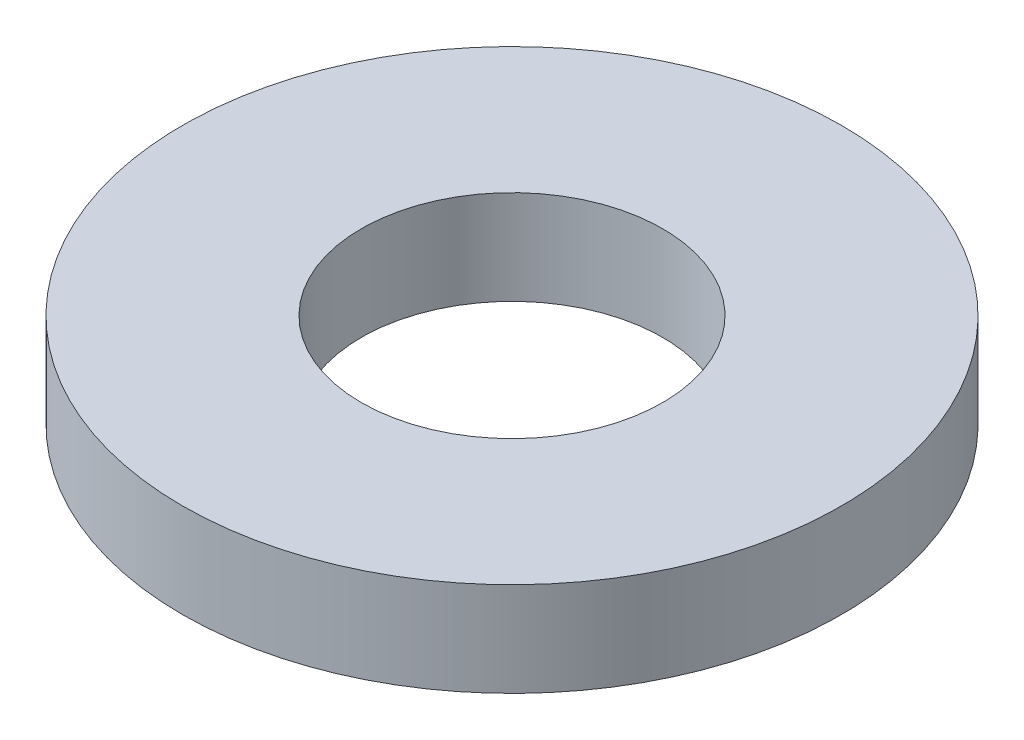
SolidWorks part; units mm, degrees
ref_plane "Front Plane" through (0, 0, 0) normal (0, 0, 1) x (1, 0, 0)
ref_plane "Top Plane" through (0, 0, 0) normal (0, 1, 0) x (1, 0, 0)
ref_plane "Right Plane" through (0, 0, 0) normal (1, 0, 0) x (0, 0, -1)
sketch "Sketch1" plane through (0, 0, 0) normal (0, 1, 0) x (1, 0, 0)
  circle A0 centre (0, 0) radius 17.5
  circle A1 centre (0, 0) radius 8
  dimension "D1" = 35
  dimension "D2" = 16
extrude "Boss-Extrude1" add sketch "Sketch1" along normal blind 5
